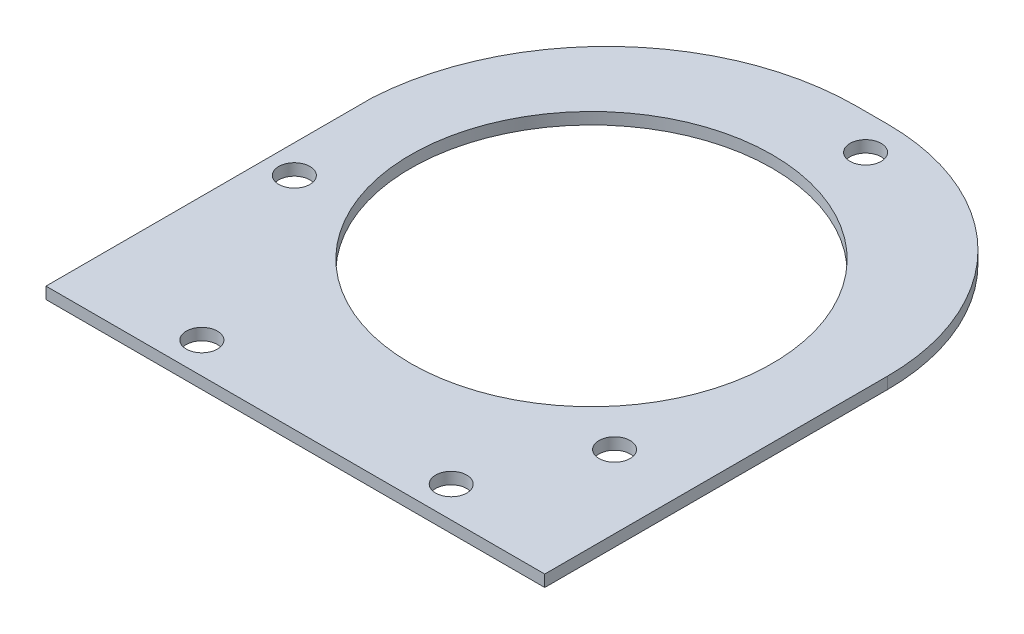
SolidWorks part; units mm, degrees
ref_plane "Front Plane" through (0, 0, 0) normal (0, 0, 1) x (1, 0, 0)
ref_plane "Top Plane" through (0, 0, 0) normal (0, 1, 0) x (1, 0, 0)
ref_plane "Right Plane" through (0, 0, 0) normal (1, 0, 0) x (0, 0, -1)
sketch "Sketch1" plane through (0, 0, 0) normal (0, 1, 0) x (1, 0, 0)
  line L0 (0, 114.3) -> (0, -114.3) construction
  line L1 (12.7, 114.3) -> (0, 114.3)
  line L2 (101.6, 25.4) -> (101.6, -114.3)
  line L3 (101.6, -114.3) -> (-101.6, -114.3)
  line L4 (-101.6, 18.6765) -> (-101.6, -114.3)
  line L5 (101.6, 114.3) -> (-101.6, -114.3) construction
  line L6 (101.6, -114.3) -> (-101.6, 114.3) construction
  line L7 (-101.6, 6.35) -> (101.6, 6.35) construction
  line L8 (0, 6.35) -> (-101.6, -28.6337) construction
  line L9 (-101.6, -101.6) -> (101.6, -101.6) construction
  circle A0 centre (0, 6.35) radius 73.66
  circle A1 centre (0, 6.35) radius 95.25 construction
  circle A2 centre (-90.0606, -24.6604) radius 6.35
  circle A3 centre (-50.8, -101.6) radius 6.35
  circle A4 centre (50.8, -101.6) radius 6.35
  circle A5 centre (18.1746, 99.85) radius 6.35
  circle A6 centre (71.8861, -56.1396) radius 6.35
  arc A7 (0, 114.3) -> (-101.6, 18.6765) centre (0, 12.5132) ccw
  arc A8 (12.7, 114.3) -> (101.6, 25.4) centre (12.7, 25.4) cw
  point P0 (0, 0)
  point P11 (0, 6.35)
  point P30 (0, 6.35)
  point P32 (0, 6.35)
  dimension "D3" = 147.32
  dimension "D5" = 190.5
  dimension "D6" = 12.7
  dimension "D7" = 12.7
  dimension "D8" = 12.7
  dimension "D11" = 88.9
  dimension "D1" = 228.6
  dimension "D2" = 120.65
  dimension "D4" = 19
  dimension "D9" = 50.8
  dimension "D10" = 203.2
extrude "Boss-Extrude1" add sketch "Sketch1" along normal blind 4.7625
sketch "Sketch2" plane through (0, 4.7625, 0) normal (0, 1, 0) x (1, 0, 0)
  line L0 (-101.6, 18.6765) -> (-101.6, -114.3) construction
  line L2 (101.6, -167.64) -> (-101.6, -167.64)
  line L5 (101.6, -167.64) -> (101.6, 114.3)
  line L6 (101.6, 114.3) -> (-101.6, 114.3)
  line L7 (-101.6, -114.3) -> (101.6, -114.3) construction
  line L8 (101.6, -114.3) -> (101.6, 25.4) construction
  line L9 (12.7, 114.3) -> (0, 114.3) construction
  line L10 (-101.6, 18.6765) -> (-101.6, -114.3)
  line L11 (-101.6, -114.3) -> (101.6, -114.3)
  line L12 (101.6, -114.3) -> (101.6, 25.4)
  line L13 (12.7, 114.3) -> (0, 114.3)
  line L14 (-101.6, -167.64) -> (-101.6, 114.3)
  line L15 (101.6, -167.64) -> (-139.7, -167.64)
  line L16 (101.6, -167.64) -> (101.6, 115.3414)
  line L17 (101.6, 115.3414) -> (-139.7, 115.3414)
  line L18 (-139.7, -167.64) -> (-139.7, 115.3414)
  point P0 (0, 0)
  dimension "D1" = 1.0414
  dimension "D2" = 53.34
  dimension "D3" = 228.6
  dimension "D4" = 203.2
  dimension "D5" = 241.3
  dimension "D6" = 282.9814
